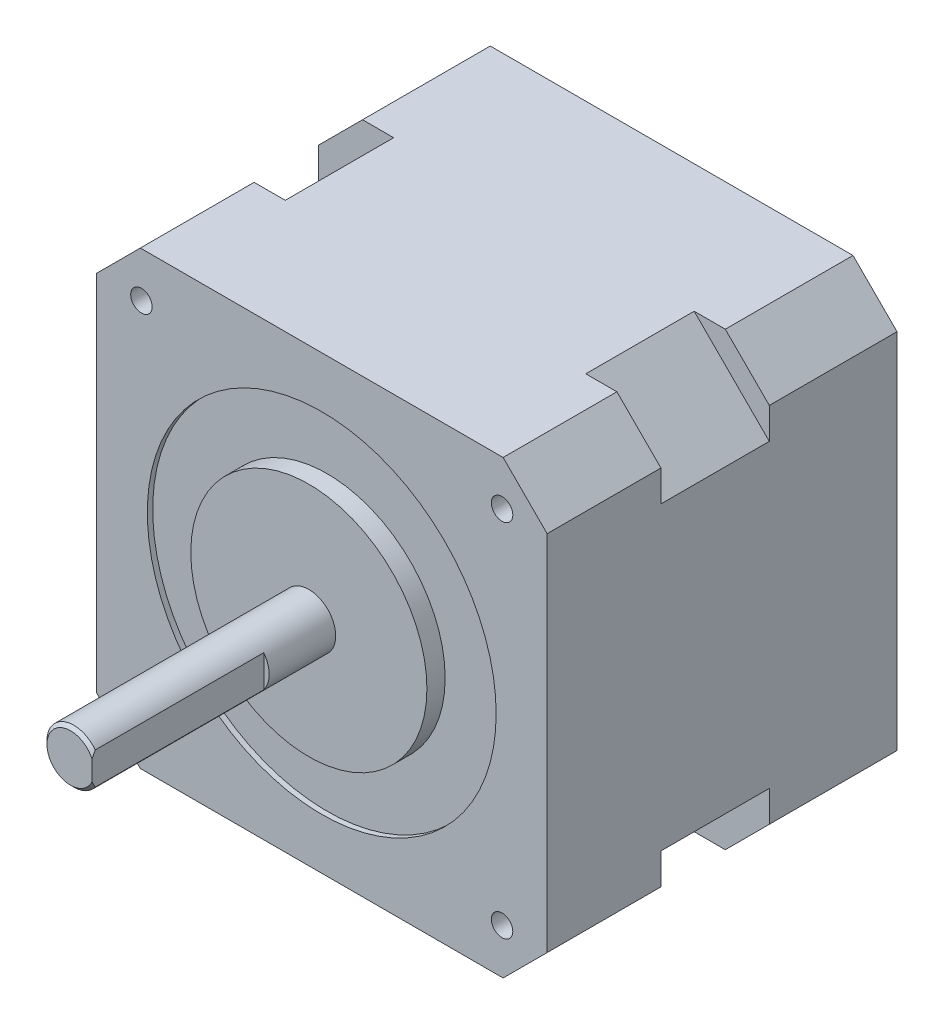
SolidWorks part; units mm, degrees
ref_plane "Plan de face" through (0, 0, 0) normal (0, 0, 1) x (1, 0, 0)
ref_plane "Plan de dessus" through (0, 0, 0) normal (0, 1, 0) x (1, 0, 0)
ref_plane "Plan de droite" through (0, 0, 0) normal (1, 0, 0) x (0, 0, -1)
sketch "Esquisse1" plane through (0, 0, 0) normal (0, 0, 1) x (1, 0, 0)
  line L0 (21, -16.9) -> (21, 16.9)
  line L1 (16.9, -21) -> (21, -16.9)
  line L2 (-16.9, 21) -> (-21, 16.9)
  line L3 (16.9, 21) -> (-16.9, 21)
  line L4 (16.9, 21) -> (21, 16.9)
  line L5 (16.9, -21) -> (-16.9, -21)
  line L6 (-16.9, -21) -> (-21, -16.9)
  line L7 (-21, -16.9) -> (-21, 16.9)
  line L8 (0, 26.608) -> (0, -33.2011) construction
  line L10 (44.1111, 0) -> (-50.7043, 0) construction
  point P2 (0, 21)
  point P4 (0, -21)
  point P10 (-21, 0)
  point P16 (21, 0)
  dimension "D1" = 21
  dimension "D2" = 16.9
  dimension "D3" = 21
  dimension "D4" = 16.9
extrude "Boss.-Extru.1" add sketch "Esquisse1" along normal blind 11.9
sketch "Esquisse2" plane through (0, 0, 11.9) normal (0, 0, 1) x (1, 0, 0)
  line L0 (14, 21) -> (21, 14)
  line L1 (16.9, 21) -> (-16.9, 21) construction
  line L2 (21, -16.9) -> (21, 16.9) construction
  line L3 (21, 14) -> (21, -14)
  line L4 (14, 21) -> (-14, 21)
  line L5 (-16.9227, 0) -> (0, 0) construction
  line L6 (0, 0) -> (0, 13.0635) construction
  line L7 (14, -21) -> (-14, -21)
  line L8 (14, -21) -> (21, -14)
  line L9 (-14, -21) -> (-21, -14)
  line L10 (-21, 14) -> (-21, -14)
  line L11 (-14, 21) -> (-21, 14)
  point P7 (-21, 0)
  point P15 (21, 0)
  point P18 (0, -21)
  point P19 (0, 21)
  dimension "D1" = 14
  dimension "D2" = 14
extrude "Boss.-Extru.2" add sketch "Esquisse2" along normal blind 10.1
sketch "Esquisse3" plane through (0, 0, 22) normal (0, 0, 1) x (1, 0, 0)
  line L0 (16.9, 21) -> (21, 16.9)
  line L1 (21, 16.9) -> (21, -16.9)
  line L2 (21, -14) -> (21, 14) construction
  line L3 (16.9, 21) -> (-16.9, 21)
  line L4 (14, 21) -> (-14, 21) construction
  line L5 (0, 8.2696) -> (0, -8.2696) construction
  line L6 (-8.1977, 0) -> (8.1977, 0) construction
  line L7 (16.9, -21) -> (-16.9, -21)
  line L8 (16.9, -21) -> (21, -16.9)
  line L9 (-16.9, -21) -> (-21, -16.9)
  line L10 (-21, 16.9) -> (-21, -16.9)
  line L11 (-16.9, 21) -> (-21, 16.9)
  point P18 (21, 0)
  point P19 (0, 0)
  point P21 (0, -21)
  point P22 (0, 21)
  point P23 (-21, 0)
extrude "Boss.-Extru.3" add sketch "Esquisse3" along normal blind 10.6
sketch "Esquisse4" plane through (0, 0, 32.6) normal (0, 0, 1) x (1, 0, 0)
  circle A0 centre (0, 0) radius 16.25
  dimension "D1" = 32.5
extrude "Enlèv. mat.-Extru.1" cut sketch "Esquisse4" against normal blind 0.5
sketch "Esquisse5" plane through (0, 0, 32.1) normal (0, 0, 1) x (1, 0, 0)
  circle A0 centre (0, 0) radius 11
  dimension "D1" = 22
extrude "Boss.-Extru.4" add sketch "Esquisse5" along normal blind 1.7
sketch "Esquisse6" plane through (0, 0, 33.8) normal (0, 0, 1) x (1, 0, 0)
  circle A0 centre (0, 0) radius 2.5
  dimension "D1" = 5
extrude "Boss.-Extru.5" add sketch "Esquisse6" along normal blind 22.2
chamfer "Chanfrein1" distance 0.3 angle 45 1 edges at (2.5, 0, 56)
sketch "Esquisse7" plane through (0, 0, 56) normal (0, 0, 1) x (1, 0, 0)
  line L0 (2, 1.5) -> (2, -1.5)
  circle A0 centre (0, 0) radius 2.5 construction
  circle A1 centre (0, 0) radius 2.5 construction
  arc A2 (2, 1.5) -> (2, -1.5) centre (0, 0) cw
  point P7 (2, 0)
  dimension "D1" = 2
extrude "Enlèv. mat.-Extru.2" cut sketch "Esquisse7" against normal blind 16
sketch "Esquisse8" plane through (0, 0, 32.6) normal (0, 0, 1) x (1, 0, 0)
  line L1 (-6.9992, 0) -> (0, 0) construction
  line L2 (0, 0) -> (0, 15.3647) construction
  line L4 (16.9, 21) -> (-16.9, 21) construction
  line L5 (-21, 16.9) -> (-21, -16.9) construction
  circle A0 centre (-16.8, 16.8) radius 1
  circle A1 centre (-16.8, -16.8) radius 1
  circle A2 centre (16.8, -16.8) radius 1
  circle A3 centre (16.8, 16.8) radius 1
  dimension "D1" = 2
  dimension "D2" = 4.2
  dimension "D3" = 4.2
extrude "Enlèv. mat.-Extru.3" cut sketch "Esquisse8" against normal blind 7
